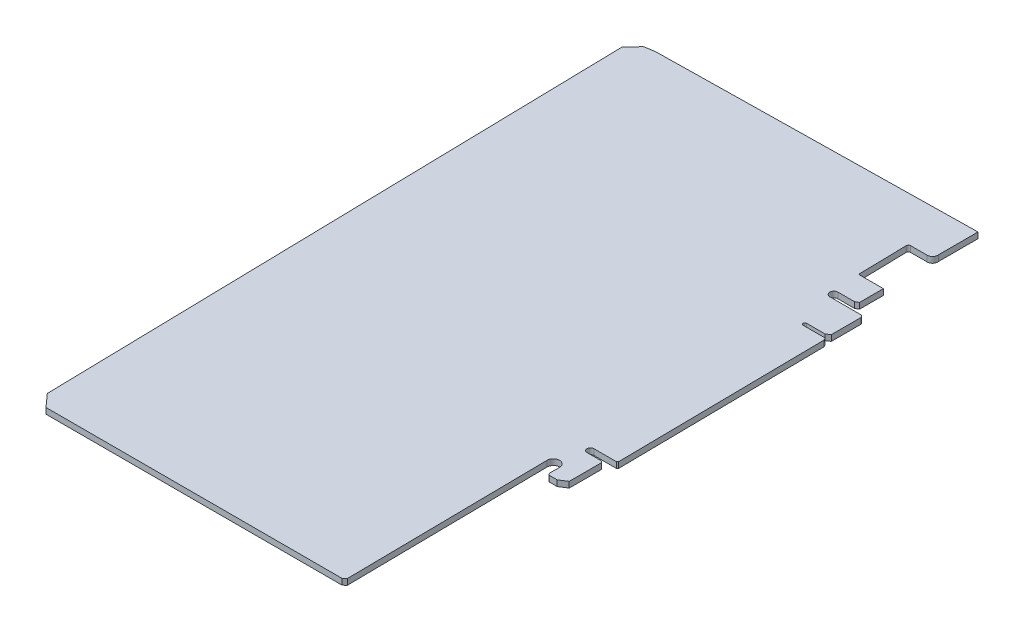
SolidWorks part; units mm, degrees
ref_plane "Front Plane" through (0, 0, 0) normal (0, 0, 1) x (1, 0, 0)
ref_plane "Top Plane" through (0, 0, 0) normal (0, 1, 0) x (1, 0, 0)
ref_plane "Right Plane" through (0, 0, 0) normal (1, 0, 0) x (0, 0, -1)
sketch "Sketch2" plane through (0, 0, 0) normal (0, 1, 0) x (1, 0, 0)
  line L0 (371.3949, 1765.0699) -> (264.2216, 1762.6805) construction
  line L1 (377.8108, 1640.3607) -> (377.7628, 1638.7277)
  line L2 (267.9905, 1778.6869) -> (264.4799, 1774.9074)
  line L3 (264.4799, 1774.9074) -> (268.7815, 1574.9756)
  line L4 (268.7815, 1574.9756) -> (272.6874, 1570.6334)
  line L5 (272.6874, 1570.6334) -> (373.4896, 1570.6334)
  line L6 (373.4896, 1570.6334) -> (374.4252, 1571.4749)
  line L7 (374.4252, 1571.4749) -> (373.5539, 1640.3333)
  line L9 (377.7628, 1638.7277) -> (377.7628, 1637.0328)
  line L10 (378.481, 1636.3146) -> (381.0343, 1636.3146)
  line L11 (381.0343, 1636.3146) -> (383.5326, 1637.9213)
  line L12 (383.5326, 1637.9213) -> (383.5326, 1648.9313)
  line L13 (383.5326, 1648.9313) -> (382.9971, 1649.4287)
  line L14 (382.9971, 1649.4287) -> (378.0714, 1649.4287)
  line L16 (386.1452, 1652.1074) -> (385.252, 1722.6952)
  line L17 (384.7174, 1723.7406) -> (377.2945, 1723.7406)
  line L18 (377.2945, 1724.9227) -> (383.5733, 1724.9227)
  line L19 (383.5733, 1724.9227) -> (384.894, 1725.7721)
  line L20 (384.894, 1725.7721) -> (384.894, 1735.6943)
  line L21 (383.9123, 1736.6759) -> (373.4896, 1736.6759)
  line L22 (373.4896, 1739.4494) -> (379.048, 1739.4494)
  line L23 (379.048, 1739.4494) -> (380.2055, 1740.0653)
  line L24 (380.2055, 1740.0653) -> (380.2055, 1748.2014)
  line L25 (380.2055, 1748.2014) -> (371.7647, 1748.2014)
  line L26 (371.7647, 1748.2014) -> (371.4089, 1764.7383)
  line L27 (372.1496, 1765.5116) -> (377.8108, 1765.5116)
  line L28 (379.5896, 1767.6083) -> (379.5896, 1781.0241)
  line L29 (379.5896, 1781.0241) -> (271.4048, 1779.2911)
  line L30 (271.4048, 1779.2911) -> (267.9905, 1778.6869)
  line L31 (378.0714, 1651.7472) -> (385.734, 1651.7472)
  line L32 (385.734, 1651.7472) -> (386.1452, 1652.1074)
  arc A0 (373.5539, 1640.3333) -> (377.8108, 1640.3607) centre (375.6822, 1640.3602) cw
  arc A2 (377.7628, 1637.0328) -> (378.481, 1636.3146) centre (378.481, 1637.0328) ccw
  arc A3 (378.0714, 1649.4287) -> (378.0714, 1651.7472) centre (378.0714, 1650.588) cw
  arc A5 (385.252, 1722.6952) -> (384.7174, 1723.7406) centre (383.9299, 1722.6785) ccw
  arc A6 (377.2945, 1723.7406) -> (377.2945, 1724.9227) centre (377.2945, 1724.3316) cw
  arc A7 (384.894, 1735.6943) -> (383.9123, 1736.6759) centre (383.9123, 1735.6943) ccw
  arc A8 (373.4896, 1736.6759) -> (373.4896, 1739.4494) centre (373.4896, 1738.0627) cw
  arc A9 (371.4089, 1764.7383) -> (372.1496, 1765.5116) centre (372.1658, 1764.7546) cw
  arc A10 (377.8108, 1765.5116) -> (379.5896, 1767.6083) centre (377.8108, 1767.3145) ccw
  dimension "D2" = 1.1593
  dimension "D3" = 1.3222
  dimension "D4" = 0.5911
  dimension "D5" = 0.9816
  dimension "D6" = 1.3868
  dimension "D7" = 0.7571
  dimension "D8" = 1.803
  dimension "D1" = 107.2
  dimension "D9" = 268.7815
  dimension "D10" = 272.6874
  dimension "D11" = 371.4089
  dimension "D12" = 371.7647
  dimension "D13" = 372.1496
  dimension "D14" = 373.4896
  dimension "D15" = 374.4252
  dimension "D16" = 383.9299
  dimension "D17" = 377.2945
  dimension "D18" = 378.0714
  dimension "D19" = 379.048
  dimension "D20" = 379.5896
  dimension "D21" = 380.2055
  dimension "D22" = 382.9971
  dimension "D23" = 383.5733
  dimension "D24" = 1648.9313
  dimension "D25" = 384.7174
  dimension "D26" = 384.894
  dimension "D27" = 1652.1074
  dimension "D28" = 385.734
  dimension "D29" = 386.1452
  dimension "D30" = 1736.6759
  dimension "D31" = 1748.2014
extrude "Boss-Extrude1" add sketch "Sketch2" along normal blind 2
